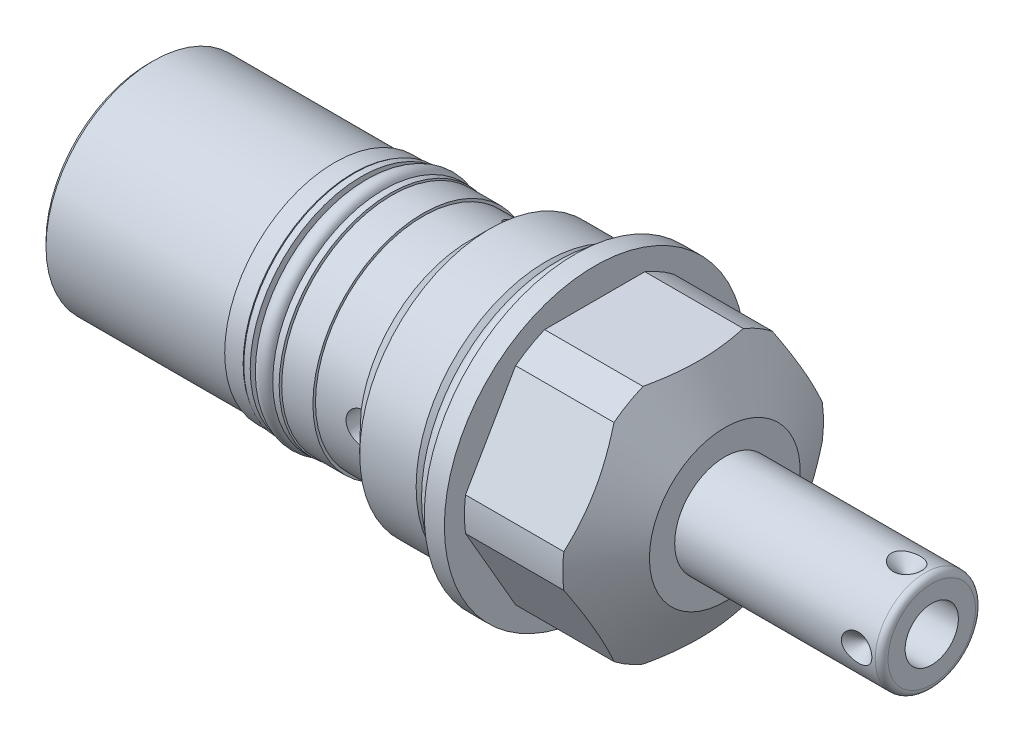
SolidWorks part; units mm, degrees
material "Alloy Steel"
ref_plane "Front Plane" through (0, 0, 0) normal (0, 0, 1) x (1, 0, 0)
ref_plane "Top Plane" through (0, 0, 0) normal (0, 1, 0) x (1, 0, 0)
ref_plane "Right Plane" through (0, 0, 0) normal (1, 0, 0) x (0, 0, -1)
ref_plane "Plane1" through (0, 0, 0) normal (1, 0, 0) x (0, 0, -1)
sketch "Sketch1" plane through (0, 0, 0) normal (1, 0, 0) x (0, 0, -1)
  circle A0 centre (0, 0) radius 23.8125
  dimension "D1" = 47.625
extrude "Extrude1" add sketch "Sketch1" along normal blind 23.7744 and the other way blind 67.4624
ref_plane "Plane2" through (0, 0, 0) normal (1, 0, 0) x (0, 0, -1)
sketch "Sketch2" plane through (0, 0, 0) normal (1, 0, 0) x (0, 0, -1)
  circle A0 centre (0, 0) radius 20.6375
  circle A1 centre (0, 0) radius 23.8125 construction
  circle A2 centre (0, 0) radius 23.8125
  dimension "D1" = 41.275
extrude "Cut-Extrude1" cut sketch "Sketch2" against normal up to next
ref_plane "Plane3" through (0, 0, 0) normal (0, 0, 1) x (1, 0, 0)
sketch "Sketch3" plane through (0, 0, 0) normal (0, 0, 1) x (1, 0, 0)
  line L0 (16.9187, 23.8125) -> (23.7744, 11.938)
  line L1 (-8.1458, 0) -> (17.0188, 0) construction
  line L2 (23.7744, 11.938) -> (23.7744, 23.8125)
  line L3 (23.7744, 23.8125) -> (16.9187, 23.8125)
  line L4 (23.7744, 23.8125) -> (0, 23.8125) construction
  dimension "D1" = 23.876
  dimension "D2" = 30
revolve "Cut-Revolve1" cut sketch "Sketch3" angle 360 about L1
ref_plane "Plane5" through (3.175, 0, 0) normal (-1, 0, 0) x (0, 0, 1)
sketch "Sketch5" plane through (3.175, 0, 0) normal (-1, 0, 0) x (0, 0, 1)
  line L0 (-10.9985, 19.05) -> (10.9985, 19.05)
  line L1 (10.9985, 19.05) -> (21.997, 0)
  line L2 (21.997, 0) -> (10.9985, -19.05)
  line L3 (10.9985, -19.05) -> (-10.9985, -19.05)
  line L4 (-10.9985, -19.05) -> (-21.997, 0)
  line L5 (-21.997, 0) -> (-10.9985, 19.05)
  line L6 (0, 0) -> (18.7904, 0) construction
  line L7 (0, 0) -> (10.9985, 19.05) construction
  line L8 (0, 0) -> (-10.9985, 19.05) construction
  circle A0 centre (0, 0) radius 23.8125 construction
  circle A1 centre (0, 0) radius 23.8125
  dimension "D1" = 38.1
  dimension "D2" = 120
  dimension "D3" = 60
extrude "Cut-Extrude3" cut sketch "Sketch5" against normal up to next
ref_plane "Plane7" through (3.175, 0, 0) normal (-1, 0, 0) x (0, 0, 1)
sketch "Sketch7" plane through (3.175, 0, 0) normal (-1, 0, 0) x (0, 0, 1)
  circle A0 centre (0, 0) radius 20.6375
  circle A1 centre (0, 0) radius 23.8125 construction
  circle A2 centre (0, 0) radius 23.8125
  dimension "D1" = 41.275
extrude "Cut-Extrude5" cut sketch "Sketch7" against normal up to next
ref_plane "Plane9" through (0, 0, 0) normal (0, 0, 1) x (1, 0, 0)
sketch "Sketch9" plane through (0, 0, 0) normal (0, 0, 1) x (1, 0, 0)
  line L0 (0, 20.6375) -> (0, 19.1389)
  line L1 (0, 19.1389) -> (-2.9718, 19.1389)
  line L2 (-2.9718, 19.1389) -> (-4.4704, 20.6375)
  line L3 (-4.4206, 0) -> (0.2105, 0) construction
  line L4 (0, 20.6375) -> (-4.4704, 20.6375)
  line L5 (0, 20.6375) -> (-67.4624, 20.6375) construction
  line L6 (0, 23.8125) -> (0, -23.8125) construction
  dimension "D1" = 2.9718
  dimension "D2" = 45
  dimension "D3" = 38.2778
revolve "Cut-Revolve3" cut sketch "Sketch9" angle 360 about L3
ref_plane "Plane10" through (0, 0, 0) normal (0, 0, 1) x (1, 0, 0)
sketch "Sketch10" plane through (0, 0, 0) normal (0, 0, 1) x (1, 0, 0)
  line L0 (-13.3985, 20.6375) -> (-16.6116, 17.4244)
  line L1 (-16.6116, 17.4244) -> (-67.4624, 17.4244)
  line L2 (-55.947, 0) -> (-8.6516, 0) construction
  line L4 (-67.4624, 20.6375) -> (-67.4624, 17.4244)
  line L5 (-4.4704, 20.6375) -> (-4.4704, -20.6375) construction
  line L6 (-4.4704, 20.6375) -> (-67.4624, 20.6375) construction
  line L7 (-13.3985, 20.6375) -> (-67.4624, 20.6375)
  dimension "D1" = 34.8488
  dimension "D2" = 45
  dimension "D3" = 8.9281
revolve "Cut-Revolve4" cut sketch "Sketch10" angle 360 about L2
ref_plane "Plane12" through (0, 0, 0) normal (0, 0, 1) x (1, 0, 0)
sketch "Sketch12" plane through (0, 0, 0) normal (0, 0, 1) x (1, 0, 0)
  line L0 (-35.0774, 17.4244) -> (-35.0774, 15.3924)
  line L1 (-35.0774, 15.3924) -> (-28.9687, 15.3924)
  line L2 (-28.9687, 15.3924) -> (-28.9687, 17.4244)
  line L3 (-31.7506, 0) -> (-25.0311, 0) construction
  line L4 (-35.0774, 17.4244) -> (-28.9687, 17.4244)
  line L5 (-16.6116, 17.4244) -> (-67.4624, 17.4244) construction
  line L6 (-67.4624, 17.4244) -> (-67.4624, -17.4244) construction
  dimension "D1" = 6.1087
  dimension "D2" = 30.7848
  dimension "D3" = 32.385
revolve "Cut-Revolve6" cut sketch "Sketch12" angle 360 about L3
ref_plane "Plane14" through (0, 0, 0) normal (0, 0, 1) x (0, -1, 0)
sketch "Sketch14" plane through (0, 0, 0) normal (0, 0, 1) x (0, -1, 0)
  line L0 (17.4244, -67.4624) -> (17.018, -67.4624)
  line L1 (17.018, -67.4624) -> (17.018, -37.9984)
  line L2 (17.018, -37.9984) -> (17.4244, -37.9984)
  line L3 (17.4244, -37.9984) -> (17.4244, -67.4624)
  line L4 (17.4244, -16.6116) -> (17.018, -16.6116)
  line L5 (17.018, -16.6116) -> (17.018, -24.0284)
  line L6 (17.018, -24.0284) -> (17.4244, -24.0284)
  line L7 (17.4244, -24.0284) -> (17.4244, -16.6116)
  line L8 (0, -55.866) -> (0, -10.3518) construction
  line L9 (17.4244, -67.4624) -> (17.4244, -35.0774) construction
  line L10 (17.4244, -28.9687) -> (17.4244, -16.6116) construction
  line L11 (-17.4244, -67.4624) -> (17.4244, -67.4624) construction
  dimension "D1" = 13.97
  dimension "D2" = 34.036
  dimension "D3" = 29.464
  dimension "D4" = 7.4168
revolve "Cut-Revolve8" cut sketch "Sketch14" angle 360 about L8
ref_plane "Plane15" through (0, 0, 0) normal (0, 0, 1) x (0, -1, 0)
sketch "Sketch15" plane through (0, 0, 0) normal (0, 0, 1) x (0, -1, 0)
  line L0 (0, -3.0937) -> (0, 0.1473) construction
  line L1 (-23.8125, 0) -> (23.8125, 0) construction
  circle A0 centre (20.6375, -1.4986) radius 1.4986
  dimension "D1" = 2.9972
  dimension "D2" = 1.4986
  dimension "D3" = 41.275
revolve "Revolve1" add sketch "Sketch15" angle 360 about L0
ref_plane "Plane16" through (0, 0, 0) normal (0, 0, 1) x (0, -1, 0)
sketch "Sketch16" plane through (0, 0, 0) normal (0, 0, 1) x (0, -1, 0)
  line L0 (15.3924, -29.2227) -> (17.5768, -29.2227)
  line L1 (17.5768, -29.2227) -> (17.5768, -30.2387)
  line L2 (17.5768, -30.2387) -> (15.3924, -30.2387)
  line L3 (15.3924, -30.2387) -> (15.3924, -29.2227)
  line L4 (15.3924, -34.8234) -> (17.5768, -34.8234)
  line L5 (17.5768, -34.8234) -> (17.5768, -33.8074)
  line L6 (17.5768, -33.8074) -> (15.3924, -33.8074)
  line L7 (15.3924, -33.8074) -> (15.3924, -34.8234)
  line L8 (0, -31.4712) -> (0, -25.3105) construction
  line L9 (-17.4244, -28.9687) -> (17.4244, -28.9687) construction
  line L10 (17.4244, -35.0774) -> (-17.4244, -35.0774) construction
  line L11 (15.3924, -35.0774) -> (15.3924, -28.9687) construction
  dimension "D1" = 1.016
  dimension "D3" = 35.1536
  dimension "D4" = 0.254
  dimension "D5" = 0.254
revolve "Revolve2" add sketch "Sketch16" angle 360 about L8
ref_plane "Plane17" through (0, 0, 0) normal (0, 0, 1) x (0, -1, 0)
sketch "Sketch17" plane through (0, 0, 0) normal (0, 0, 1) x (0, -1, 0)
  line L0 (0, -31.7506) -> (0, -25.0311) construction
  line L1 (17.5768, -33.8074) -> (-17.5768, -33.8074) construction
  circle A0 centre (16.7005, -32.0231) radius 1.3081
  point P0 (9.8298, -25.3365)
  point P1 (9.8298, -31.4452)
  dimension "D1" = 2.6162
  dimension "D2" = 33.401
  dimension "D3" = 1.7843
revolve "Revolve3" add sketch "Sketch17" angle 360 about L0
ref_plane "Plane18" through (0, 0, 0) normal (0, 0, 1) x (0, -1, 0)
sketch "S2D0001" plane through (0, 0, 0) normal (0, 0, 1) x (0, -1, 0)
  line L0 (0, 23.7744) -> (-7.9375, 23.7744)
  line L1 (-7.9375, 23.7744) -> (-7.9375, 55.5244)
  line L2 (-6.9215, 56.5404) -> (0, 56.5404)
  line L3 (0, 56.5404) -> (0, 23.7744)
  line L4 (0, 7.2658) -> (0, 37.3443) construction
  line L5 (11.938, 23.7744) -> (-11.938, 23.7744) construction
  line L6 (-23.8125, 0) -> (23.8125, 0) construction
  arc A0 (-6.9215, 56.5404) -> (-7.9375, 55.5244) centre (-6.9215, 55.5244) ccw
  dimension "D2" = 1.016
  dimension "D1" = 15.875
  dimension "D3" = 56.5404
revolve "Revolve4" add sketch "S2D0001" angle 360 about L4
ref_plane "Plane19" through (36.322, -2.8067, 0) normal (0, 0, 1) x (0, -1, 0)
sketch "Sketch19" plane through (36.322, -2.8067, 0) normal (0, 0, 1) x (0, -1, 0)
  line L0 (1.4097, 20.2184) -> (1.4097, 4.9784)
  line L1 (1.4097, 4.9784) -> (-2.8067, 2.4449)
  line L2 (1.4097, 20.2184) -> (-2.8067, 20.2184)
  line L3 (-2.8067, 20.2184) -> (-2.8067, 2.4449)
  line L4 (-2.8067, -18.6227) -> (-2.8067, 0.5923) construction
  line L5 (4.1148, 20.2184) -> (-9.7282, 20.2184) construction
  dimension "D1" = 8.4328
  dimension "D2" = 15.24
  dimension "D3" = 59
revolve "Cut-Revolve9" cut sketch "Sketch19" angle 360 about L4
ref_plane "Plane20" through (32.3596, 0, -5.5562) normal (0, 1, 0) x (1, 0, 0)
sketch "S2D0002" plane through (32.3596, 0, -5.5562) normal (0, 1, 0) x (1, 0, 0)
  line L0 (20.2184, 2.3813) -> (22.6314, 2.3813)
  line L1 (22.6314, 2.3813) -> (20.2184, -0.0317)
  line L2 (20.2184, 2.3813) -> (20.2184, -0.0317)
  line L3 (20.2184, -3.3652) -> (20.2184, 0.0794) construction
  line L4 (23.1648, 2.3813) -> (-8.5852, 2.3813) construction
  line L5 (24.1808, -12.4777) -> (24.1808, 1.3652) construction
  dimension "D1" = 3.9624
  dimension "D2" = 45
  dimension "D3" = 4.826
revolve "Cut-Revolve10" cut sketch "S2D0002" angle 360 about L3
pattern_circular "CirPattern1" count 4 over 360 about axis through (7.2658, 0, 0) along (-1, 0, 0) of "Cut-Revolve10"
chamfer "Chamfer1" distance 0.762 angle 45 1 edges at (-67.4624, 0, 17.018)
sketch "Sketch23" plane through (0, 0, 0) normal (0, 0, 1) x (1, 0, 0)
  line L0 (-67.4624, 16.256) -> (-67.4624, -16.256) construction
  circle A0 centre (-16.6624, 0) radius 2.5273
  dimension "D1" = 5.0546
  dimension "D2" = 50.8
extrude "Cut-Extrude7" cut sketch "Sketch23" along normal through all
sketch "Sketch24" plane through (0, 0, 0) normal (0, 0, 1) x (1, 0, 0)
  line L0 (0, 0) -> (-56.0091, 0) construction
  line L1 (-67.4624, 6.1849) -> (-64.9097, 5.6423)
  line L2 (-67.4624, 16.256) -> (-67.4624, -16.256) construction
  line L3 (-64.9097, 5.6423) -> (-64.2458, 4.9784)
  line L4 (-64.2458, 4.9784) -> (-53.1876, 4.9784)
  line L5 (-53.1876, 4.9784) -> (-53.1876, 0)
  line L6 (-53.1876, 0) -> (-67.4624, 0)
  line L7 (-67.4624, 0) -> (-67.4624, 6.1849)
  dimension "D1" = 9.9568
  dimension "D2" = 14.2748
  dimension "D3" = 45
  dimension "D4" = 12
  dimension "D5" = 12.3698
  dimension "D6" = 2.5527
revolve "Cut-Revolve11" cut sketch "Sketch24" angle 360 about L0
sketch "Sketch25" plane through (-67.4624, 0, 0) normal (-1, 0, 0) x (0, 0, 1)
  circle A0 centre (0, 0) radius 13.0302
extrude "Extrude2" add sketch "Sketch25" along normal blind 0.508
sketch "Sketch26" plane through (-67.9704, 0, 0) normal (-1, 0, 0) x (0, 0, 1)
  circle A0 centre (0, 0) radius 6.1849
extrude "Cut-Extrude8" cut sketch "Sketch26" against normal blind 0.508
pattern_circular "CirPattern2" count 3 over 360 about axis through (7.2658, 0, 0) along (-1, 0, 0) of "Cut-Extrude7"
